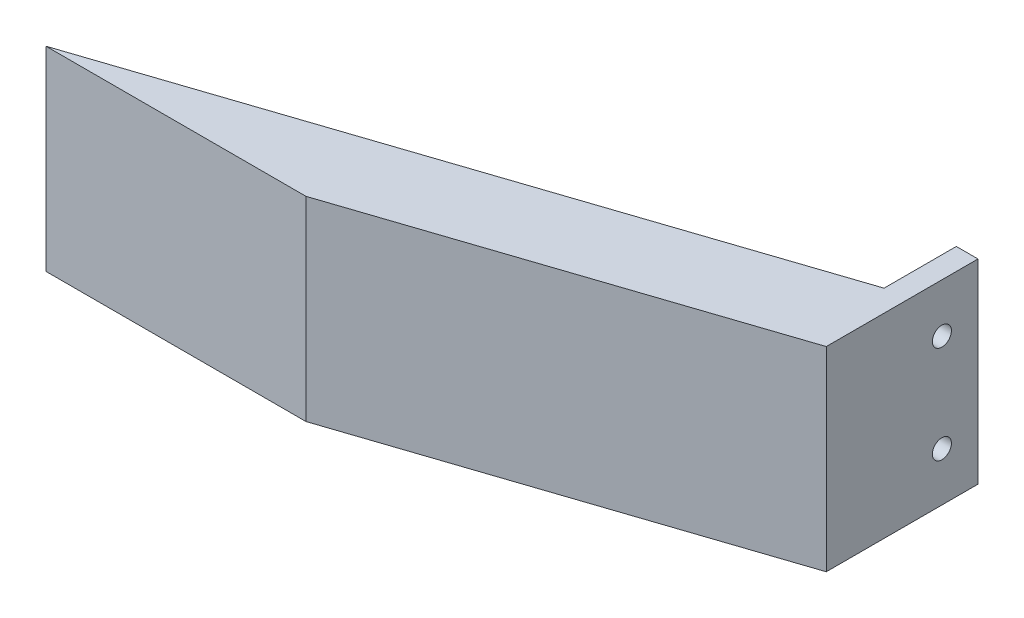
SolidWorks part; units mm, degrees
ref_plane "Front Plane" through (0, 0, 0) normal (0, 0, 1) x (1, 0, 0)
ref_plane "Top Plane" through (0, 0, 0) normal (0, 1, 0) x (1, 0, 0)
ref_plane "Right Plane" through (0, 0, 0) normal (1, 0, 0) x (0, 0, -1)
sketch "Sketch1" plane through (0, 0, 0) normal (0, 1, 0) x (1, 0, 0)
  line L0 (0, 0) -> (150, 0)
  line L5 (150, 0) -> (150, 50)
  line L6 (0, 0) -> (150, 50)
  line L7 (150, 50) -> (150, 30)
  line L8 (150, 30) -> (59.9741, 0)
  dimension "D1" = 150
  dimension "D2" = 50
  dimension "D3" = 20
  dimension "D4" = 71.57
extrude "Boss-Extrude1" add sketch "Sketch1" along normal blind 45 contours L8 L5 L6 L0
sketch "Sketch2" plane through (150, 0, 0) normal (1, 0, 0) x (0, 0, -1)
  line L1 (30, 45) -> (65, 45)
  line L2 (30, 45) -> (30, 0)
  line L3 (30, 0) -> (65, 0)
  line L4 (65, 45) -> (65, 0)
  dimension "D1" = 45
  dimension "D2" = 35
extrude "Boss-Extrude2" add sketch "Sketch2" against normal blind 5
sketch "Sketch3" plane through (145, 0, 0) normal (-1, 0, 0) x (0, 0, 1)
  line L0 (-65, 45) -> (-65, 22.5)
  line L1 (-65, 0) -> (-65, 45) construction
  line L2 (-65, 22.5) -> (-65, 0)
  circle A0 centre (-56.6667, 33.75) radius 2.2
  circle A1 centre (-56.6667, 11.25) radius 2.2
  dimension "D1" = 4.4
  dimension "D2" = 4.4
extrude "Cut-Extrude1" cut sketch "Sketch3" against normal blind 5 contours A1 | A0
